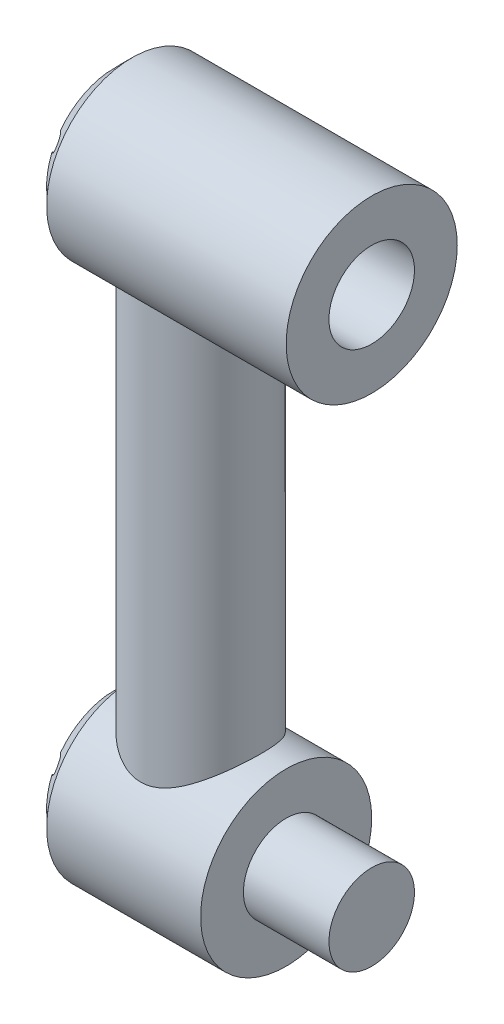
SolidWorks part; units mm, degrees
ref_plane "Front Plane" through (0, 0, 0) normal (0, 0, 1) x (1, 0, 0)
ref_plane "Top Plane" through (0, 0, 0) normal (0, 1, 0) x (1, 0, 0)
ref_plane "Right Plane" through (0, 0, 0) normal (1, 0, 0) x (0, 0, -1)
sketch "Sketch1" plane through (0, 0, 0) normal (0, 1, 0) x (1, 0, 0)
  circle A0 centre (0, 0) radius 88.9
  dimension "D1" = 177.8
extrude "Boss-Extrude1" add sketch "Sketch1" along normal mid plane 635
sketch "Sketch4" plane through (0, 0, 0) normal (1, 0, 0) x (0, 0, -1)
  line L0 (0, 317.5) -> (0, 495.3)
  line L1 (88.9, 317.5) -> (-88.9, 317.5) construction
  line L2 (0, -317.5) -> (0, -469.9)
  line L3 (-88.9, -317.5) -> (88.9, -317.5) construction
  circle A0 centre (0, 406.4) radius 127
  circle A1 centre (0, -393.7) radius 127
  dimension "D2" = 254
  dimension "D4" = 254
  dimension "D1" = 177.8
  dimension "D3" = 152.4
extrude "Boss-Extrude2" add sketch "Sketch4" along normal mid plane 254
sketch "Sketch5" plane through (127, 0, 0) normal (1, 0, 0) x (0, 0, -1)
  circle A0 centre (0, -393.7) radius 63.5
  circle A1 centre (0, -393.7) radius 127 construction
  dimension "D2" = 127
  dimension "D1" = 63.5
extrude "Boss-Extrude3" add sketch "Sketch5" along normal blind 127
sketch "Sketch6" plane through (127, 0, 0) normal (1, 0, 0) x (0, 0, -1)
  circle A0 centre (0, 406.4) radius 63.5
  circle A1 centre (0, 406.4) radius 127
  circle A2 centre (0, 406.4) radius 127
  dimension "D2" = 127
  dimension "D1" = 0
extrude "Boss-Extrude4" add sketch "Sketch6" along normal blind 127
chamfer "Chamfer1" distance 25.4 angle 45 2 edges at (-127, -393.7, -127) (-127, 406.4, -127)
sketch "Sketch7" plane through (-127, 0, 0) normal (-1, 0, 0) x (0, 0, 1)
  circle A0 centre (0, 508) radius 12.7
  circle A1 centre (0, 406.4) radius 101.6 construction
  circle A7 centre (87.9882, 457.2) radius 12.7
  circle A8 centre (87.9882, 355.6) radius 12.7
  circle A9 centre (0, 304.8) radius 12.7
  circle A10 centre (-87.9882, 355.6) radius 12.7
  circle A11 centre (-87.9882, 457.2) radius 12.7
  circle A12 centre (0, -292.1) radius 12.7
  circle A13 centre (0, -393.7) radius 101.6 construction
  circle A14 centre (87.9882, -342.9) radius 12.7
  circle A15 centre (87.9882, -444.5) radius 12.7
  circle A16 centre (0, -495.3) radius 12.7
  circle A17 centre (-87.9882, -444.5) radius 12.7
  circle A18 centre (-87.9882, -342.9) radius 12.7
  point P9 (0, 0)
  point P23 (0, 406.4)
  point P33 (0, -393.7)
  dimension "D1" = 25.4
  dimension "D3" = 6
  dimension "D2" = 25.4
  dimension "D4" = 6
extrude "Cut-Extrude1" cut sketch "Sketch7" against normal blind 25.4
